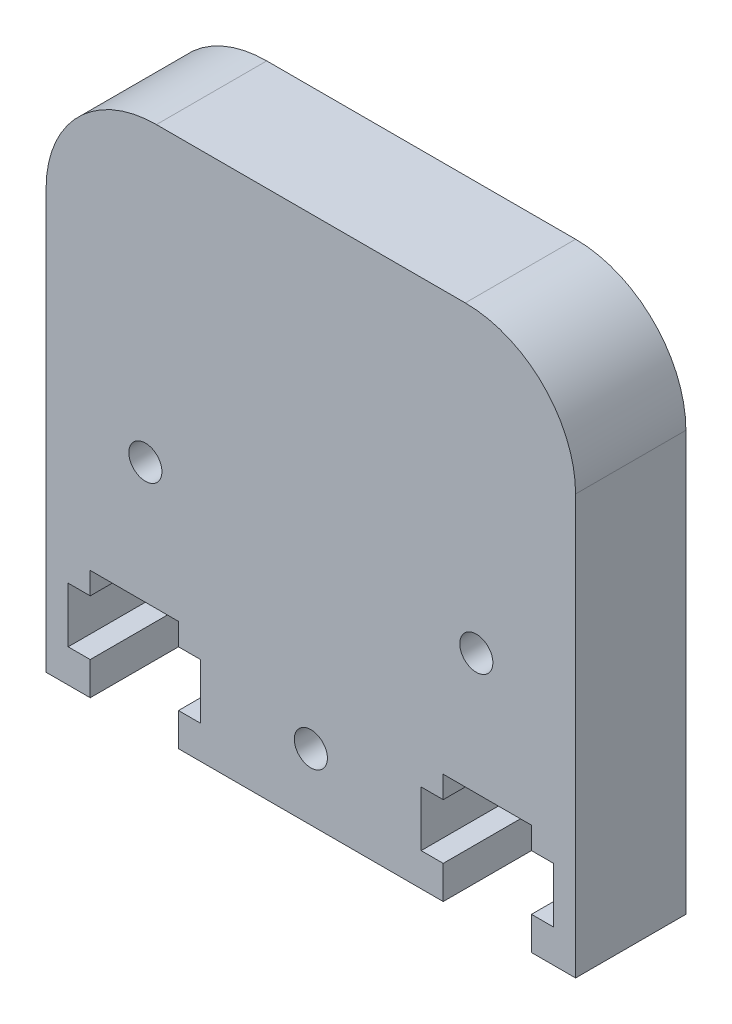
SolidWorks part; units mm, degrees
ref_plane "Front Plane" through (0, 0, 0) normal (0, 0, 1) x (1, 0, 0)
ref_plane "Top Plane" through (0, 0, 0) normal (0, 1, 0) x (1, 0, 0)
ref_plane "Right Plane" through (0, 0, 0) normal (1, 0, 0) x (0, 0, -1)
sketch "Sketch1" plane through (0, 0, 0) normal (0, 0, 1) x (1, 0, 0)
  line L0 (0, 19.2238) -> (0, -18.8976) construction
  line L2 (-12, 12) -> (12, 12)
  line L3 (-12, 12) -> (-12, -12)
  line L4 (-12, -12) -> (12, -12)
  line L5 (12, 12) -> (12, -12)
  line L6 (-12, 12) -> (12, -12) construction
  line L7 (-19.713, -1.5) -> (18.6381, -1.5) construction
  line L8 (-12, -12) -> (12, 12) construction
  circle A0 centre (0, -9) radius 0.75
  circle A1 centre (-7.5, -1.5) radius 0.75
  circle A2 centre (7.5, -1.5) radius 0.75
  circle A3 centre (0, -1.5) radius 7.5 construction
  point P1 (0, 0)
  dimension "D3" = 1.5
  dimension "D5" = 1.5
  dimension "D6" = 1.5
  dimension "D1" = 24
  dimension "D2" = 0
  dimension "D4" = 3
  dimension "D7" = 7.5
  dimension "D8" = 7.5
extrude "Boss-Extrude1" add sketch "Sketch1" along normal blind 5
fillet "Fillet1" radius 5 2 edges at (-12, 12, 2.5) (12, 12, 2.5)
sketch "Sketch2" plane through (0, 0, 5) normal (0, 0, 1) x (1, 0, 0)
  line L0 (0, 0) -> (0, -16.3479) construction
  line L1 (-8, -7) -> (-8, -17) construction
  line L2 (-10, -12) -> (-10, -10.5)
  line L3 (-12, -12) -> (12, -12) construction
  line L4 (-10, -10.5) -> (-11, -10.5)
  line L5 (-11, -10.5) -> (-11, -8)
  line L6 (-11, -8) -> (-10, -8)
  line L7 (-10, -8) -> (-10, -7)
  line L8 (-10, -7) -> (-6, -7)
  line L9 (-6, -7) -> (-6, -8)
  line L10 (-6, -8) -> (-5, -8)
  line L11 (-5, -8) -> (-5, -10.5)
  line L12 (-5, -10.5) -> (-6, -10.5)
  line L13 (-6, -10.5) -> (-6, -12)
  line L14 (-10, -12) -> (-6, -12)
  line L15 (-12, 7) -> (-12, -12) construction
  point P9 (-8, -12)
  point P21 (-8, -7)
  dimension "D1" = 8
  dimension "D2" = 1
  dimension "D3" = 4
  dimension "D4" = 1.5
  dimension "D5" = 1
  dimension "D6" = 24
  dimension "D7" = 4
  dimension "D8" = 5
  dimension "D9" = 19
extrude "Cut-Extrude1" cut sketch "Sketch2" against normal blind 5
mirror "Mirror1" about plane through (0, 0, 0) normal (1, 0, 0) of "Cut-Extrude1"
